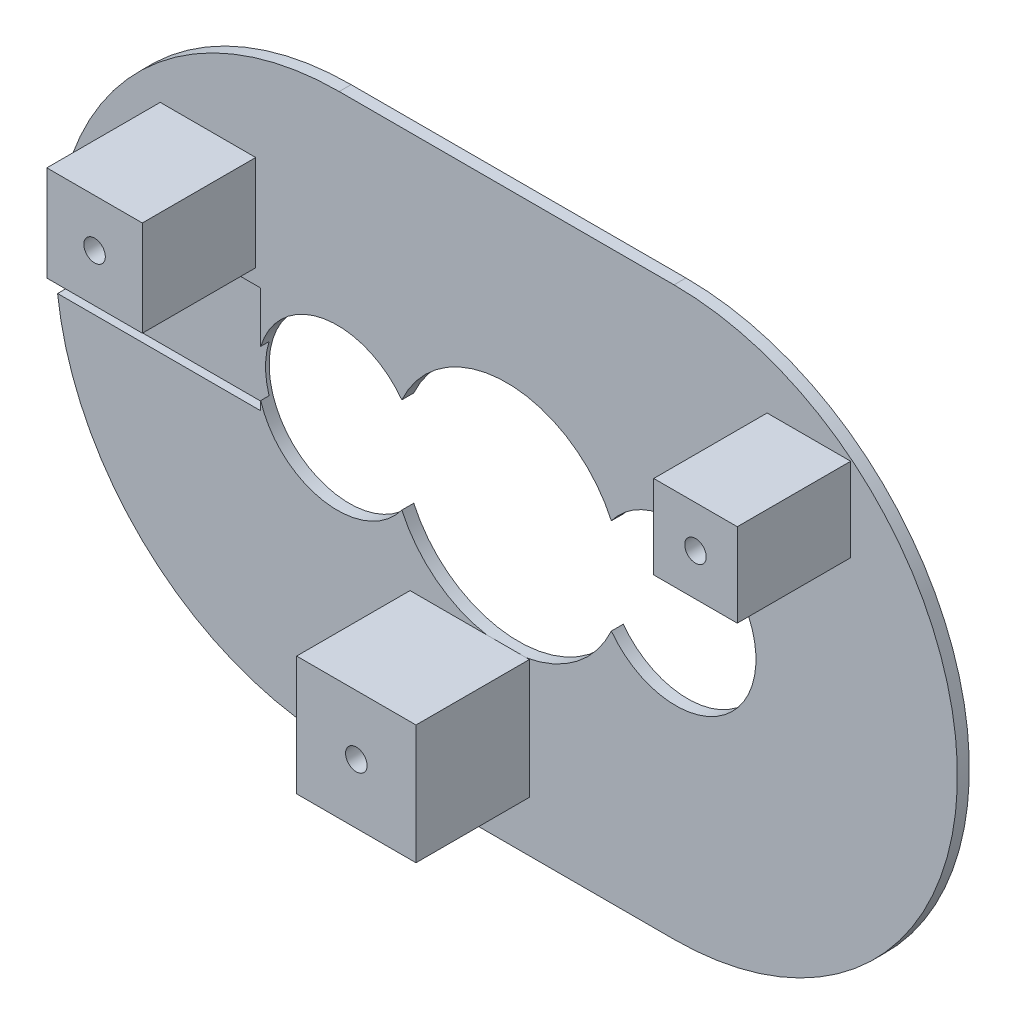
SolidWorks part; units mm, degrees
ref_plane "Front Plane" through (0, 0, 0) normal (0, 0, 1) x (1, 0, 0)
ref_plane "Top Plane" through (0, 0, 0) normal (0, 1, 0) x (1, 0, 0)
ref_plane "Right Plane" through (0, 0, 0) normal (1, 0, 0) x (0, 0, -1)
sketch "Sketch1" plane through (0, 0, 0) normal (0, 0, 1) x (1, 0, 0)
  line L2 (-14.0267, 23.7456) -> (14.0267, 23.7456)
  line L3 (14.0267, -23.7456) -> (-14.0267, -23.7456)
  arc A0 (14.0267, -23.7456) -> (14.0267, 23.7456) centre (14.0267, 0) ccw
  arc A2 (20.4935, 0.0542) -> (20.1382, 2.0896) centre (10.5176, -0.6387) ccw construction
  arc A3 (-14.0267, 23.7456) -> (-14.0267, -23.7456) centre (-14.0267, 0) ccw
  circle A4 centre (0, 0) radius 9.6448
  circle A6 centre (14.176, 0) radius 6.3177 construction
  circle A7 centre (-14.176, 0) radius 6.3177 construction
  circle A8 centre (-14.176, 0) radius 6.5177
  circle A9 centre (14.176, 0) radius 6.5177
  dimension "D1" = 0.2
extrude "Boss-Extrude1" add sketch "Sketch1" along normal blind 1
sketch "Sketch2" plane through (0, 0, 1) normal (0, 0, 1) x (1, 0, 0)
  line L0 (-29.0187, 15.4623) -> (-21.0187, 15.4623)
  line L1 (-8.0902, -9.4975) -> (1.9098, -9.4975)
  line L2 (-8.0902, -9.4975) -> (-8.0902, -19.4975)
  line L3 (-8.0902, -19.4975) -> (1.9098, -19.4975)
  line L4 (1.9098, -9.4975) -> (1.9098, -19.4975)
  line L5 (-8.0902, -9.4975) -> (1.9098, -19.4975) construction
  line L6 (-8.0902, -19.4975) -> (1.9098, -9.4975) construction
  line L7 (-29.0187, 15.4623) -> (-29.0187, 7.4623)
  line L8 (-29.0187, 7.4623) -> (-21.0187, 7.4623)
  line L9 (-21.0187, 15.4623) -> (-21.0187, 7.4623)
  line L10 (-29.0187, 15.4623) -> (-21.0187, 7.4623) construction
  line L11 (-29.0187, 7.4623) -> (-21.0187, 15.4623) construction
  line L12 (21.8271, 18.3469) -> (28.8271, 18.3469)
  line L13 (21.8271, 18.3469) -> (21.8271, 11.3469)
  line L14 (21.8271, 11.3469) -> (28.8271, 11.3469)
  line L15 (28.8271, 18.3469) -> (28.8271, 11.3469)
  line L16 (21.8271, 18.3469) -> (28.8271, 11.3469) construction
  line L17 (21.8271, 11.3469) -> (28.8271, 18.3469) construction
  point P0 (-3.0902, -14.4975)
  point P5 (-25.0187, 11.4623)
  point P10 (25.3271, 14.8469)
  dimension "D1" = 10
  dimension "D2" = 10
  dimension "D3" = 8
  dimension "D4" = 8
  dimension "D5" = 7
  dimension "D6" = 7
extrude "Boss-Extrude2" add sketch "Sketch2" along normal blind 9.5
sketch "Sketch3" plane through (0, 0, 10.5) normal (0, 0, 1) x (1, 0, 0)
  line L0 (-29.0187, 15.4623) -> (-21.0187, 7.4623) construction
  line L1 (-21.0187, 15.4623) -> (-29.0187, 7.4623) construction
  line L2 (21.8271, 18.3469) -> (28.8271, 11.3469) construction
  line L3 (28.8271, 18.3469) -> (21.8271, 11.3469) construction
  line L4 (-8.0902, -9.4975) -> (1.9098, -19.4975) construction
  line L5 (1.9098, -9.4975) -> (-8.0902, -19.4975) construction
  circle A0 centre (-25.0187, 11.4623) radius 0.9
  circle A1 centre (25.3271, 14.8469) radius 0.9
  circle A2 centre (-3.0902, -14.4975) radius 0.9
  dimension "D1" = 1.8
extrude "Cut-Extrude1" cut sketch "Sketch3" against normal blind 8
sketch "Sketch4" plane through (0, 0, 1) normal (0, 0, 1) x (1, 0, 0)
  line L0 (-20.6, 6.2) -> (-36.9486, 6.2) construction
  line L1 (-37.6177, -2.7053) -> (-20.6, -2.7053) construction
  line L2 (-20.6, -2.7053) -> (-20.6, 6.2) construction
  line L3 (-20.6, 6.2) -> (-36.9486, 6.2)
  line L4 (-37.6177, -2.7053) -> (-20.6, -2.7053)
  line L5 (-20.6, -2.7053) -> (-20.6, 6.2)
  arc A0 (-14.0267, 23.7456) -> (-14.0267, -23.7456) centre (-14.0267, 0) ccw construction
  arc A1 (-36.9486, 6.2) -> (-37.6177, -2.7053) centre (-14.0267, 0) ccw
extrude "Cut-Extrude2" cut sketch "Sketch4" against normal blind 0.7
sketch "Sketch6" plane through (0, 0, 1) normal (0, 0, 1) x (1, 0, 0)
  circle A2 centre (-14.176, 0) radius 6.3177 construction
  circle A3 centre (14.176, 0) radius 6.3177 construction
  circle A4 centre (14.176, 0) radius 6.7177
  circle A5 centre (-14.176, 0) radius 6.7177
  dimension "D1" = 0.4
extrude "Cut-Extrude7" cut sketch "Sketch6" against normal through all both and the other way through all
